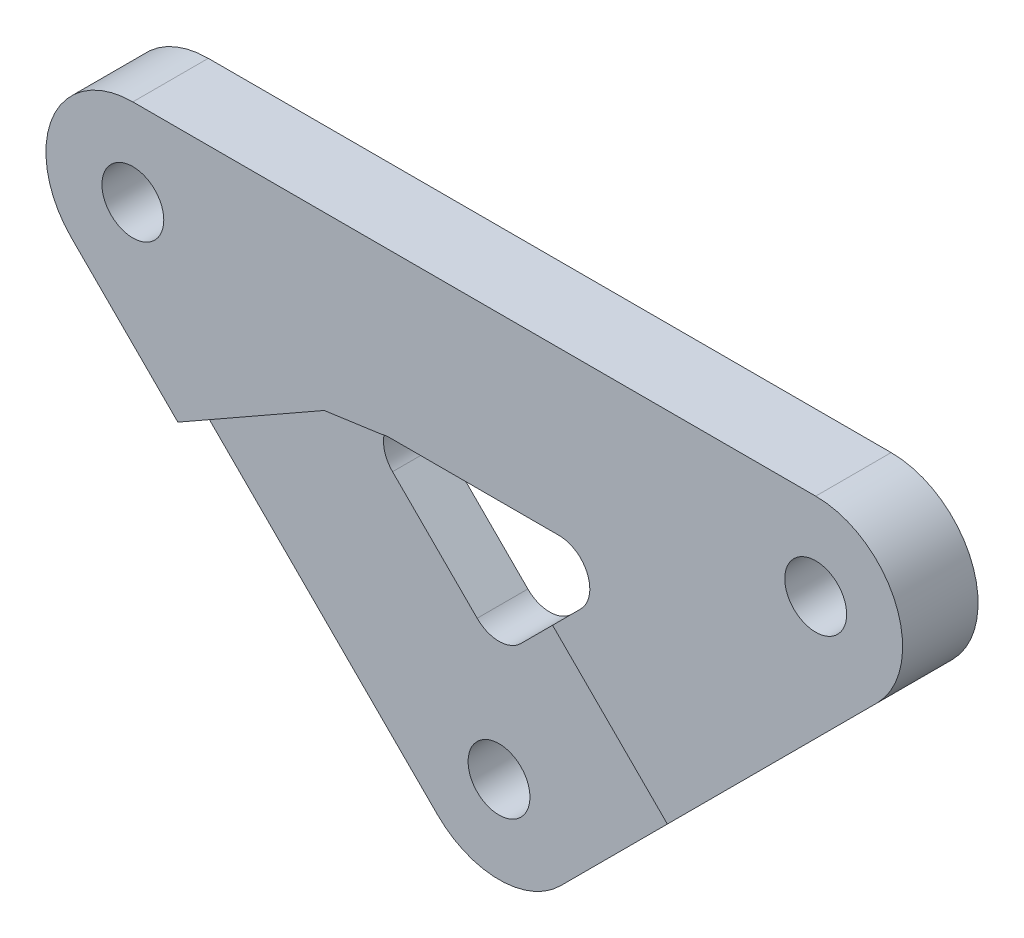
SolidWorks part; units mm, degrees
material "Acrílico (Impacto medio-alto)"
ref_plane "Piano frontale" through (0, 0, 0) normal (0, 0, 1) x (1, 0, 0)
ref_plane "Piano superiore" through (0, 0, 0) normal (0, 1, 0) x (1, 0, 0)
ref_plane "Piano destro" through (0, 0, 0) normal (1, 0, 0) x (0, 0, -1)
sketch "Schizzo1" plane through (0, 0, 0) normal (0, 0, 1) x (1, 0, 0)
  line L0 (0, -9.7873) -> (0, 53.0062) construction
  line L1 (-36.5346, 28.388) -> (-22.6274, 28.388) construction
  line L2 (22.6274, 28.388) -> (36.5346, 28.388) construction
  line L3 (36.5346, 28.388) -> (26.7007, 18.5541) construction
  line L4 (22.6274, 28.388) -> (-22.6274, 28.388)
  line L5 (4.0733, -4.0733) -> (26.7007, 18.5541)
  line L6 (5.6072, 17.6274) -> (-5.6072, 17.6274)
  line L7 (-7.0568, 14.1278) -> (-1.4496, 8.5206)
  line L8 (1.4496, 8.5206) -> (7.0568, 14.1278)
  line L9 (-26.7007, 18.5541) -> (-4.0733, -4.0733)
  line L10 (4.0733, -4.0733) -> (0, -8.1467) construction
  line L11 (0, -8.1467) -> (-4.0733, -4.0733) construction
  line L12 (-36.5346, 28.388) -> (-26.7007, 18.5541) construction
  line L13 (-22.6274, 22.6274) -> (0, 0) construction
  line L14 (0, 0) -> (22.6274, 22.6274) construction
  line L15 (22.6274, 22.6274) -> (-22.6274, 22.6274) construction
  circle A0 centre (0, 0) radius 2.05
  arc A1 (-4.0733, -4.0733) -> (4.0733, -4.0733) centre (0, 0) ccw
  circle A2 centre (22.6274, 22.6274) radius 2.05
  circle A3 centre (-22.6274, 22.6274) radius 2.05
  arc A4 (-26.7007, 18.5541) -> (-22.6274, 28.388) centre (-22.6274, 22.6274) cw
  arc A5 (22.6274, 28.388) -> (26.7007, 18.5541) centre (22.6274, 22.6274) cw
  arc A6 (-1.4496, 8.5206) -> (1.4496, 8.5206) centre (0, 9.9702) ccw
  arc A7 (5.6072, 17.6274) -> (7.0568, 14.1278) centre (5.6072, 15.5774) cw
  arc A8 (-5.6072, 17.6274) -> (-7.0568, 14.1278) centre (-5.6072, 15.5774) ccw
  point P13 (0, 7.0711)
  point P23 (10.5563, 17.6274)
  point P29 (-10.5563, 17.6274)
  dimension "D4" = 4.1
  dimension "D5" = 5
  dimension "D6" = 2.05
  dimension "D9" = 32
  dimension "D10" = 32
  dimension "D2" = 5
  dimension "D11" = 90
extrude "Estrusione-Estrusione1" add sketch "Schizzo1" along normal blind 5
sketch "Sketch2" plane through (0, 0, 5) normal (0, 0, 1) x (1, 0, 0)
  line L2 (4.0733, -4.0733) -> (26.7007, 18.5541) construction
  line L3 (12.7973, 4.6506) -> (0, -8.1467)
  line L4 (-26.7007, 18.5541) -> (-4.0733, -4.0733) construction
  line L5 (0, -8.1467) -> (-19.6438, 11.4972)
  line L6 (-19.6438, 11.4972) -> (-9.9463, 17.0174)
  line L7 (-7.0568, 14.1278) -> (-1.4496, 8.5206) construction
  line L8 (-9.9463, 17.0174) -> (-1.4496, 8.5206) construction
  line L9 (-1.4496, 8.5206) -> (1.4496, 8.5206)
  line L11 (-9.9463, 17.0174) -> (-5.6072, 17.6274)
  line L12 (-5.6072, 17.6274) -> (-1.4496, 8.5206)
  line L16 (1.4496, 8.5206) -> (5.1884, 12.2595)
  line L17 (1.4496, 8.5206) -> (7.0568, 14.1278) construction
  line L18 (5.1884, 12.2595) -> (12.7973, 4.6506)
extrude "Cut-Extrude2" cut sketch "Sketch2" against normal blind 1.64
